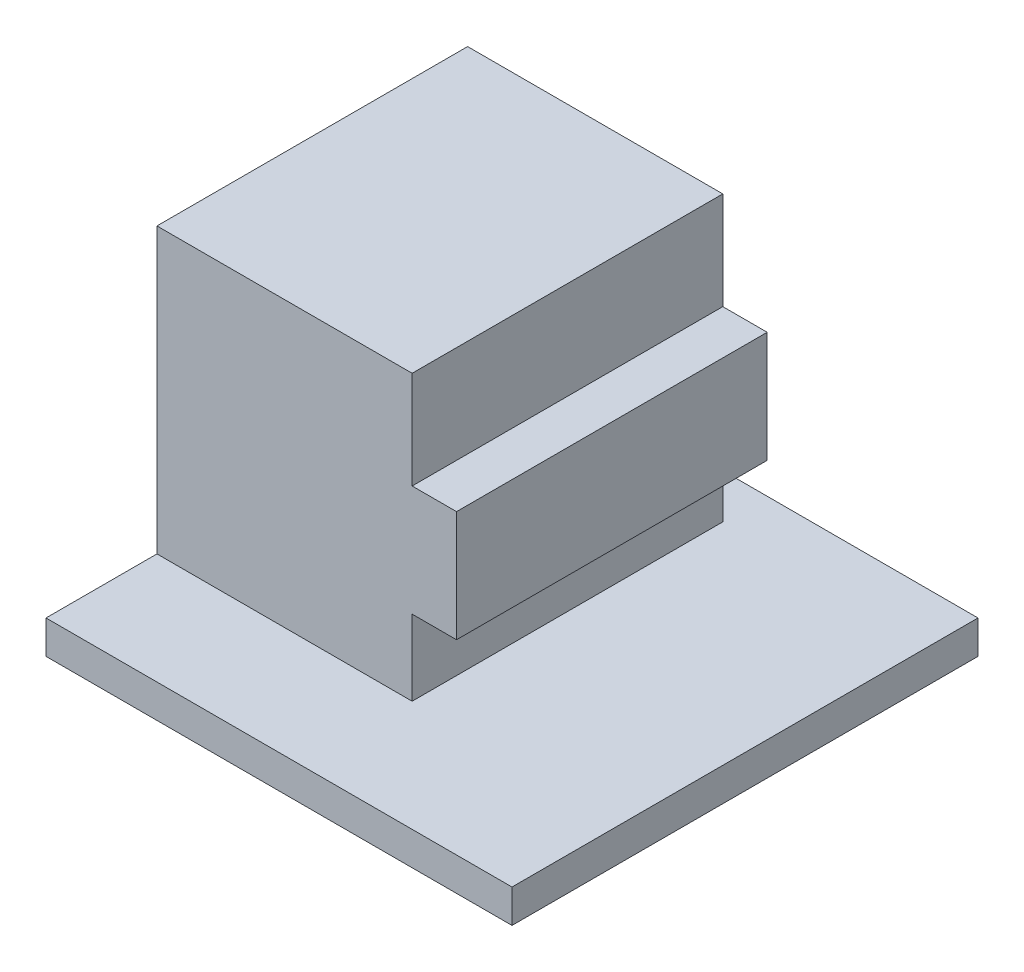
SolidWorks part; units mm, degrees
ref_plane "Front Plane" through (0, 0, 0) normal (0, 0, 1) x (1, 0, 0)
ref_plane "Top Plane" through (0, 0, 0) normal (0, 1, 0) x (1, 0, 0)
ref_plane "Right Plane" through (0, 0, 0) normal (1, 0, 0) x (0, 0, -1)
sketch "Sketch1" plane through (0, 0, 0) normal (0, 1, 0) x (1, 0, 0)
  line L1 (0, 0) -> (21, 0)
  line L2 (0, 0) -> (0, 21)
  line L3 (0, 21) -> (21, 21)
  line L4 (21, 0) -> (21, 21)
  dimension "D1" = 21
  dimension "D2" = 21
extrude "Boss-Extrude1" add sketch "Sketch1" along normal blind 1.5
ref_plane "Plane1" through (0, 0, -19) normal (0, 0, -1) x (-1, 0, 0)
sketch "Sketch3" plane through (0, 0, -19) normal (0, 0, -1) x (-1, 0, 0)
  line L0 (0, 1.5) -> (0, 14.3)
  line L1 (0, 1.5) -> (0, 0) construction
  line L2 (0, 1.5) -> (-21, 1.5) construction
  line L3 (0, 14.3) -> (-11.5, 14.3)
  line L4 (-11.5, 14.3) -> (-11.5, 9.9)
  line L5 (-11.5, 9.9) -> (-13.5, 9.9)
  line L6 (-13.5, 9.9) -> (-13.5, 4.9)
  line L7 (-13.5, 4.9) -> (-11.5, 4.9)
  line L8 (-11.5, 4.9) -> (-11.5, 1.5)
  line L9 (-11.5, 1.5) -> (0, 1.5)
  dimension "D1" = 12.8
  dimension "D2" = 11.5
  dimension "D3" = 4.4
  dimension "D4" = 2
  dimension "D5" = 5
extrude "Boss-Extrude3" add sketch "Sketch3" against normal blind 14
